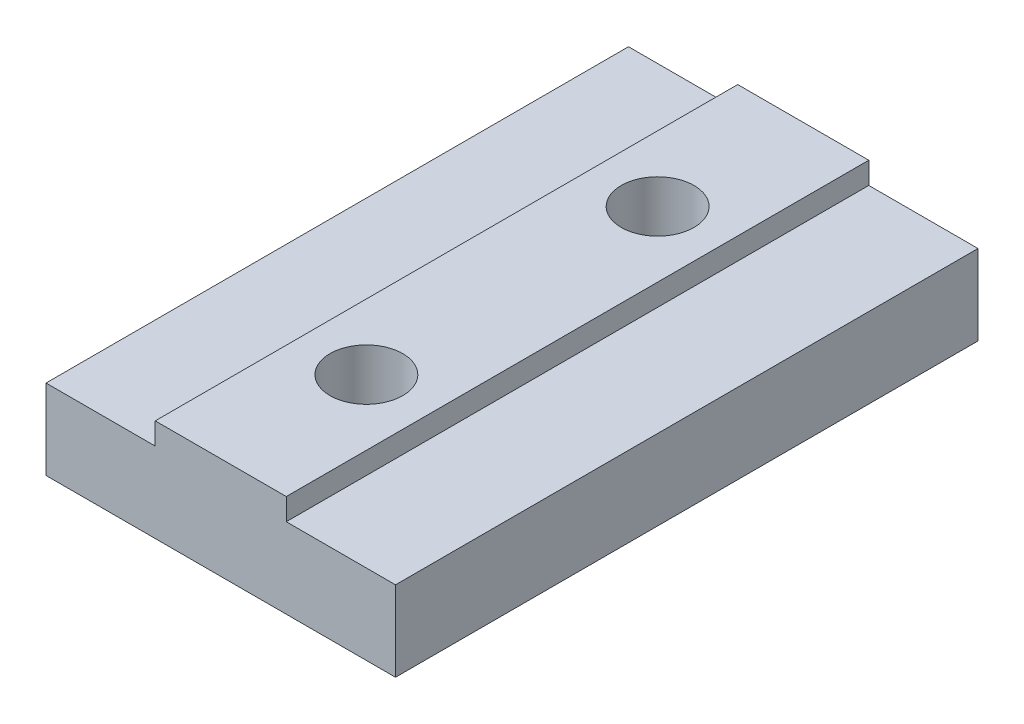
SolidWorks part; units mm, degrees
ref_plane "Plan de face" through (0, 0, 0) normal (0, 0, 1) x (1, 0, 0)
ref_plane "Plan de dessus" through (0, 0, 0) normal (0, 1, 0) x (1, 0, 0)
ref_plane "Plan de droite" through (0, 0, 0) normal (1, 0, 0) x (0, 0, -1)
sketch "Esquisse1" plane through (0, 0, 0) normal (0, 0, 1) x (1, 0, 0)
  line L0 (24, 5.5) -> (16.5, 5.5)
  line L1 (0, 0) -> (24, 0)
  line L2 (0, 0) -> (0, 5.5)
  line L4 (24, 0) -> (24, 5.5)
  line L5 (16.5, 5.5) -> (16.5, 7)
  line L6 (16.5, 7) -> (7.5, 7)
  line L7 (7.5, 7) -> (7.5, 5.5)
  line L8 (7.5, 5.5) -> (0, 5.5)
  line L9 (12, 0) -> (12, 14.355) construction
  point P11 (6.8432, 7)
  dimension "D1" = 24
  dimension "D2" = 5.5
  dimension "D3" = 1.5
  dimension "D4" = 1.5
  dimension "D5" = 9
extrude "Boss.-Extru.1" add sketch "Esquisse1" along normal blind 40
sketch "Esquisse2" plane through (0, 7, 0) normal (0, 1, 0) x (1, 0, 0)
  line L0 (12, 0) -> (12, -40) construction
  line L1 (16.5, 0) -> (7.5, 0) construction
  line L2 (16.5, -40) -> (7.5, -40) construction
  circle A0 centre (12, -10) radius 2.5
  circle A1 centre (12, -30) radius 2.5
  dimension "D1" = 5
  dimension "D2" = 5
  dimension "D3" = 20
  dimension "D4" = 10
extrude "Enlèv. mat.-Extru.1" cut sketch "Esquisse2" against normal through all
